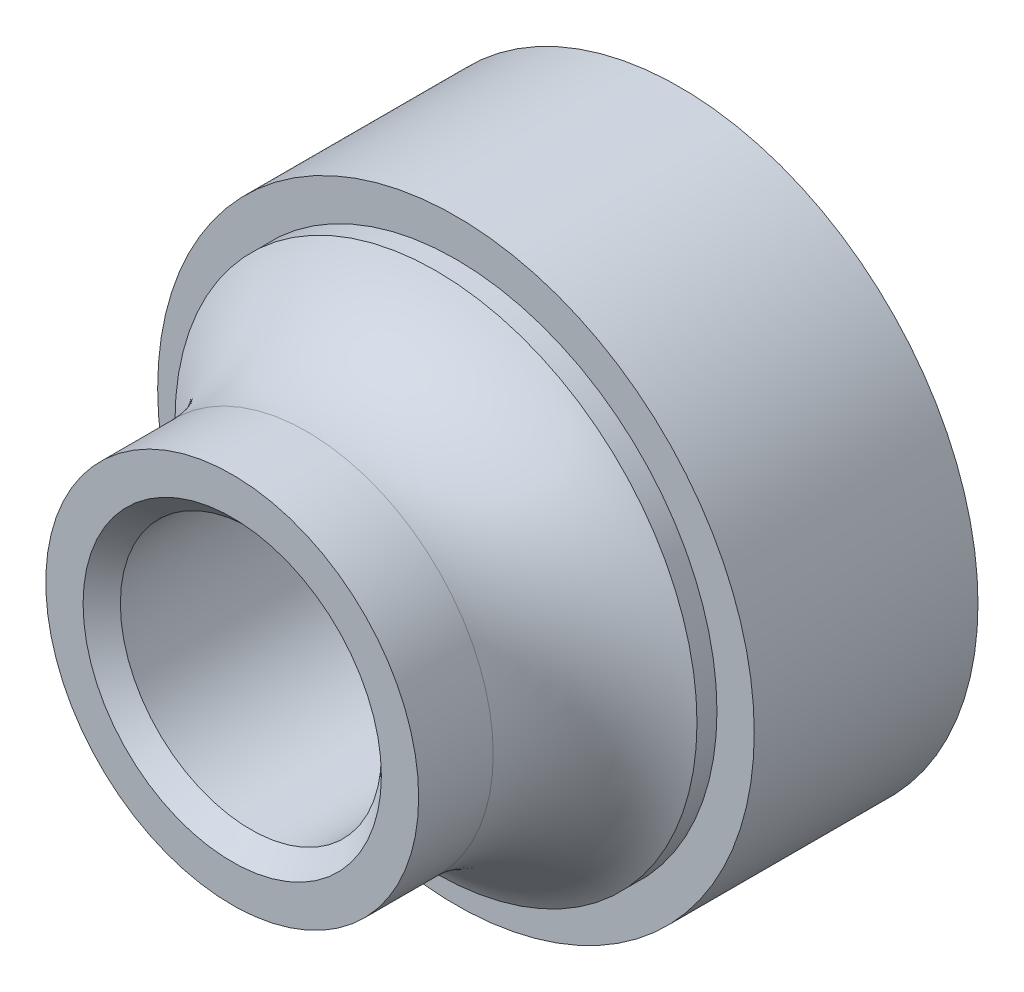
SolidWorks part; units mm, degrees
ref_plane "Спереди" through (0, 0, 0) normal (0, 0, 1) x (1, 0, 0)
ref_plane "Сверху" through (0, 0, 0) normal (0, 1, 0) x (1, 0, 0)
ref_plane "Справа" through (0, 0, 0) normal (1, 0, 0) x (0, 0, -1)
sketch "Эскиз1" plane through (0, 0, 0) normal (0, 0, 1) x (1, 0, 0)
  circle A0 centre (0, 0) radius 8
  dimension "D1" = 16
extrude "Вытянуть1" add sketch "Эскиз1" along normal blind 6
sketch "Эскиз2" plane through (0, 0, 6) normal (0, 0, 1) x (1, 0, 0)
  circle A0 centre (0, 0) radius 7
  dimension "D1" = 14
extrude "Вытянуть2" add sketch "Эскиз2" along normal blind 6
sketch "Эскиз3" plane through (0, 0, 0) normal (1, 0, 0) x (0, 0, -1)
  line L0 (-6, 8) -> (-6, -8) construction
  line L1 (-12, 7) -> (-12, -7) construction
  line L2 (-10, 5) -> (-12, 5)
  line L3 (-12, 5) -> (-12, 7)
  line L4 (-12, 7) -> (-6.5359, 7)
  line L5 (-6, 7) -> (-12, 7) construction
  line L6 (-12, 0) -> (0, 0) construction
  arc A0 (-10, 5) -> (-6.5359, 7) centre (-10, 9) ccw
  dimension "D3" = 8
  dimension "D1" = 4
  dimension "D2" = 9
revolve "Вырез-Повернуть1" cut sketch "Эскиз3" angle 360 about L6
sketch "Эскиз4" plane through (0, 0, 0) normal (0, 0, -1) x (-1, 0, 0)
  circle A0 centre (0, 0) radius 3.5
  dimension "D1" = 7
extrude "Вырез-Вытянуть1" cut sketch "Эскиз4" against normal blind 96
cosmetic thread "Условное изображение резьбы2" parameters "D2"=8
chamfer "Фаска1" distance 0.5 angle 45 2 edges at (3.5, 0, 12) (-3.5, 0, 0)
